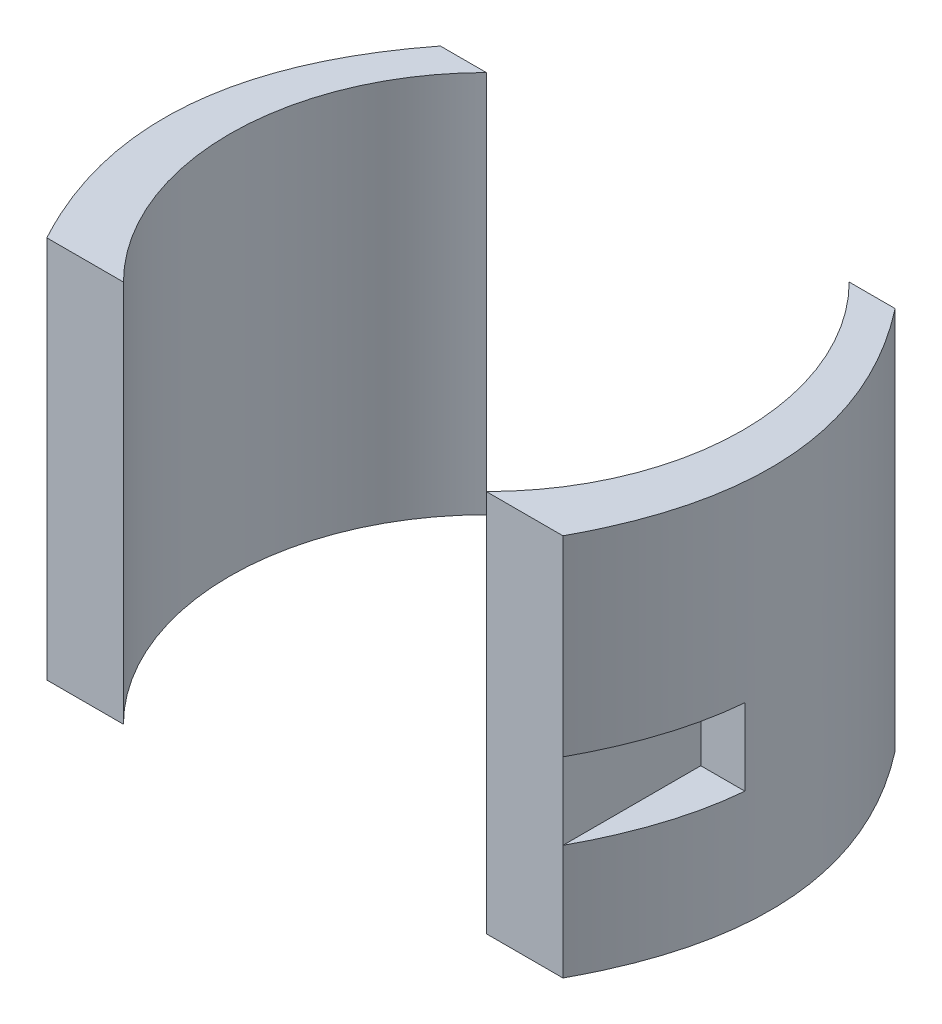
SolidWorks part; units mm, degrees
ref_plane "Front Plane" through (0, 0, 0) normal (0, 0, 1) x (1, 0, 0)
ref_plane "Top Plane" through (0, 0, 0) normal (0, 1, 0) x (1, 0, 0)
ref_plane "Right Plane" through (0, 0, 0) normal (1, 0, 0) x (0, 0, -1)
sketch "Sketch2" plane through (0, 0, 0) normal (0, 1, 0) x (1, 0, 0)
  line L0 (0, 0) -> (-23.6881, 23.6881) construction
  line L1 (0, 0) -> (-23.6881, -23.6881) construction
  line L2 (-23.6881, 23.6881) -> (-29.6881, 23.6881)
  line L3 (-23.6881, -23.6881) -> (-33.6881, -23.6881)
  line L4 (-33.5, 0) -> (-39.5, 0) construction
  line L5 (0, 33.5) -> (0, -33.5) construction
  line L6 (33.5, 0) -> (39.5, 0) construction
  line L7 (23.6881, -23.6881) -> (33.6881, -23.6881)
  line L8 (23.6881, 23.6881) -> (29.6881, 23.6881)
  circle A0 centre (0, 0) radius 33.5
  spline S0 degree 2 poles (-29.6881, 23.6881) (-47.2217, 1.1836) (-33.6881, -23.6881) knots 0 0 0 1 1 1
  spline S1 degree 2 poles (29.6881, 23.6881) (47.2217, 1.1836) (33.6881, -23.6881) knots 0 0 0 1 1 1
  dimension "D1" = 67
  dimension "D2" = 6
  dimension "D3" = 6
  dimension "D4" = 10
extrude "Boss-Extrude1" add sketch "Sketch2" along normal blind 50
sketch "Sketch3" plane through (0, 0, 23.6881) normal (0, 0, 1) x (1, 0, 0)
  line L1 (-33.6881, 25) -> (-41.6881, 25)
  line L2 (-33.6881, 25) -> (-33.6881, 15)
  line L3 (-33.6881, 15) -> (-41.6881, 15)
  line L4 (-41.6881, 25) -> (-41.6881, 15)
  line L5 (-23.6881, 0) -> (-33.6881, 0) construction
  line L6 (-23.6881, 50) -> (-23.6881, 0) construction
  line L7 (-23.6881, 50) -> (23.6881, 50) construction
  line L8 (-23.6881, 0) -> (23.6881, 0) construction
  line L9 (0, 50) -> (0, 0) construction
  line L10 (33.6881, 25) -> (33.6881, 15)
  line L11 (33.6881, 15) -> (41.6881, 15)
  line L12 (41.6881, 25) -> (41.6881, 15)
  line L13 (33.6881, 25) -> (41.6881, 25)
  dimension "D2" = 15
  dimension "D3" = 10
  dimension "D4" = 8
extrude "Cut-Extrude5" cut sketch "Sketch3" against normal blind 18
